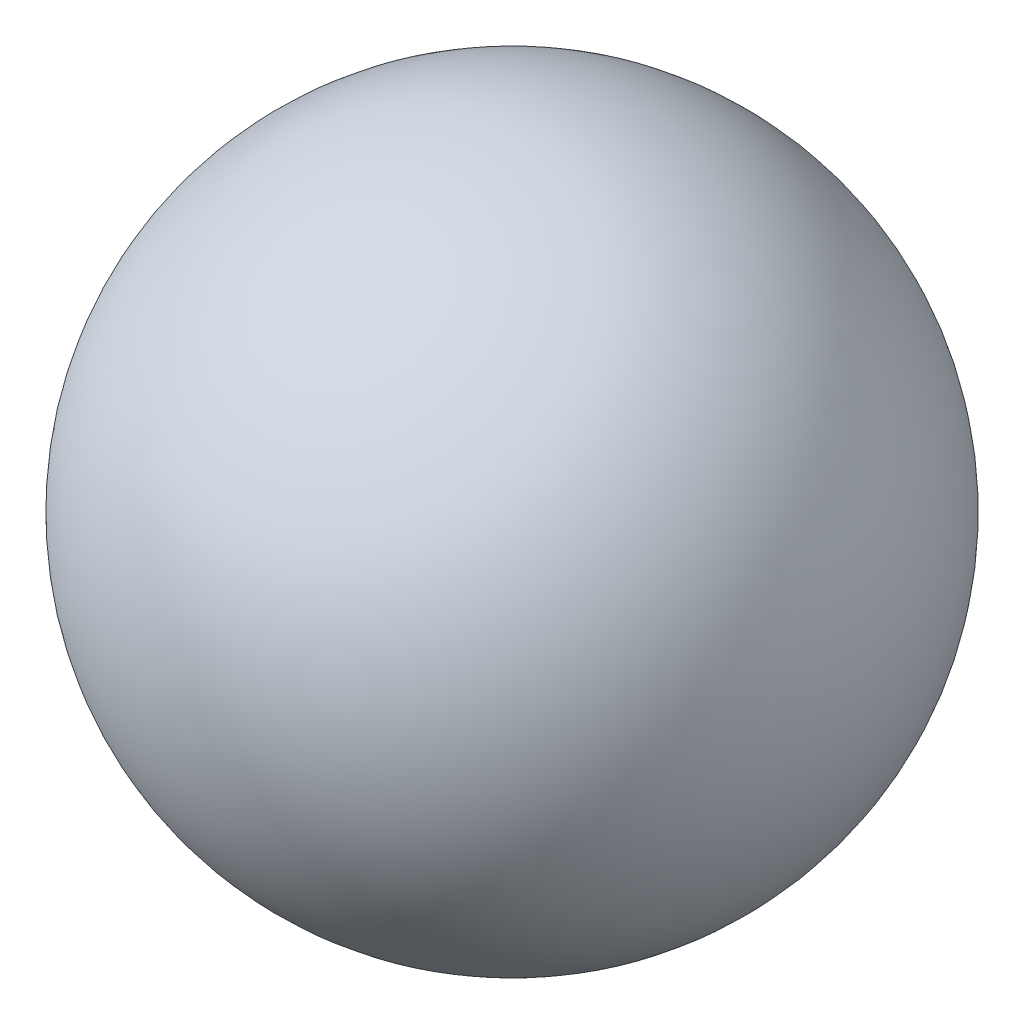
SolidWorks part; units mm, degrees
ref_plane "Front" through (0, 0, 0) normal (0, 0, 1) x (1, 0, 0)
ref_plane "Top" through (0, 0, 0) normal (0, 1, 0) x (1, 0, 0)
ref_plane "Right" through (0, 0, 0) normal (1, 0, 0) x (0, 0, -1)
sketch "Sketch1" plane through (0, 0, 0) normal (0, 0, 1) x (1, 0, 0)
  line L0 (0, 330.2) -> (0, 0)
  circle A0 centre (0, 165.1) radius 165.1
  point P5 (76.9896, -126.32)
  point P6 (-5.1326, 165.6703)
  dimension "D1" = 330.2
revolve "Revolve1" add sketch "Sketch1" angle 360 about L0
